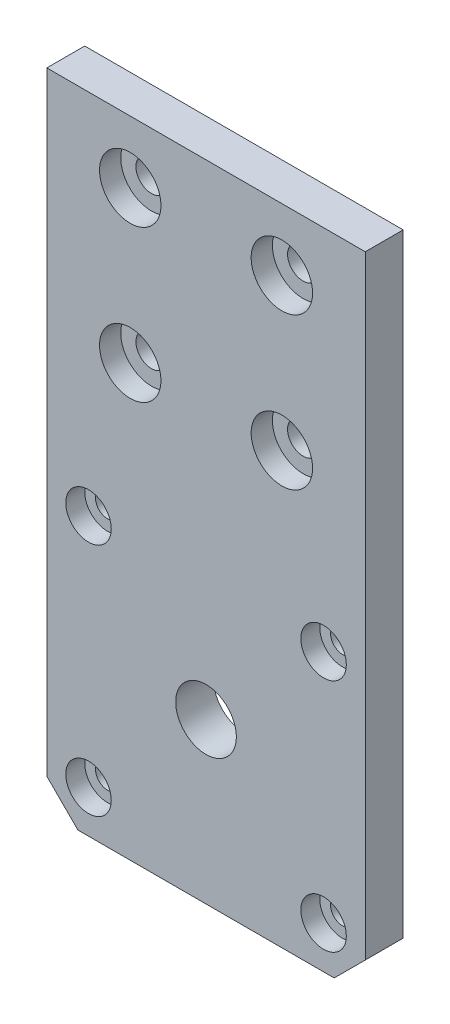
SolidWorks part; units mm, degrees
ref_plane "Alzado" through (0, 0, 0) normal (0, 0, 1) x (1, 0, 0)
ref_plane "Planta" through (0, 0, 0) normal (0, 1, 0) x (1, 0, 0)
ref_plane "Vista lateral" through (0, 0, 0) normal (1, 0, 0) x (0, 0, -1)
sketch "Croquis1" plane through (0, 0, 0) normal (0, 0, 1) x (1, 0, 0)
  line L0 (11, 56.8) -> (31, 76.8) construction
  line L1 (0, 85) -> (42, 85)
  line L2 (0, 85) -> (0, 0)
  line L3 (0, 0) -> (42, 0)
  line L4 (42, 85) -> (42, 0)
  line L5 (21, 66.8) -> (21, 85) construction
  circle A0 centre (11, 76.8) radius 2.05
  circle A1 centre (31, 76.8) radius 2.05
  circle A4 centre (31, 56.8) radius 2.05
  circle A5 centre (11, 56.8) radius 2.05
  dimension "D3" = 4.1
  dimension "D1" = 42
  dimension "D2" = 85
  dimension "D4" = 20
  dimension "D6" = 8.2
  dimension "D7" = 20
extrude "Saliente-Extruir1" add sketch "Croquis1" along normal blind 5
sketch "Croquis4" plane through (0, 0, 5) normal (0, 0, 1) x (1, 0, 0)
  circle A0 centre (11, 76.8) radius 4.05
  circle A1 centre (11, 56.8) radius 4.05
  circle A2 centre (31, 56.8) radius 4.05
  circle A3 centre (31, 76.8) radius 4.05
  dimension "D1" = 8.1
extrude "Cortar-Extruir1" cut sketch "Croquis4" against normal blind 2.8
sketch "Croquis5" plane through (0, 0, 5) normal (0, 0, 1) x (1, 0, 0)
  line L0 (5.5, 36.58) -> (36.5, 5.58) construction
  line L1 (0, 85) -> (42, 85) construction
  line L2 (36.5, 36.58) -> (5.5, 5.58) construction
  line L3 (21, 21.08) -> (21, 0) construction
  line L4 (0, 0) -> (42, 0) construction
  circle A0 centre (21, 21.08) radius 11.5 construction
  circle A1 centre (5.5, 36.58) radius 1.575
  circle A2 centre (36.5, 36.58) radius 1.575
  circle A3 centre (36.5, 5.58) radius 1.575
  circle A4 centre (5.5, 5.58) radius 1.575
  circle A5 centre (21, 21.08) radius 4
  dimension "D1" = 23
  dimension "D4" = 3.15
  dimension "D2" = 31
  dimension "D3" = 31
  dimension "D5" = 63.92
extrude "Cortar-Extruir2" cut sketch "Croquis5" against normal through all
sketch "Croquis6" plane through (0, 0, 5) normal (0, 0, 1) x (1, 0, 0)
  circle A0 centre (5.5, 36.58) radius 3
  circle A1 centre (36.5, 36.58) radius 3
  circle A2 centre (36.5, 5.58) radius 3
  circle A4 centre (5.5, 5.58) radius 3
  dimension "D1" = 6
extrude "Cortar-Extruir3" cut sketch "Croquis6" against normal blind 2.5
chamfer "Chaflán1" distance 4.1 angle 45 2 edges at (42, 0, 2.5) (0, 0, 2.5)
